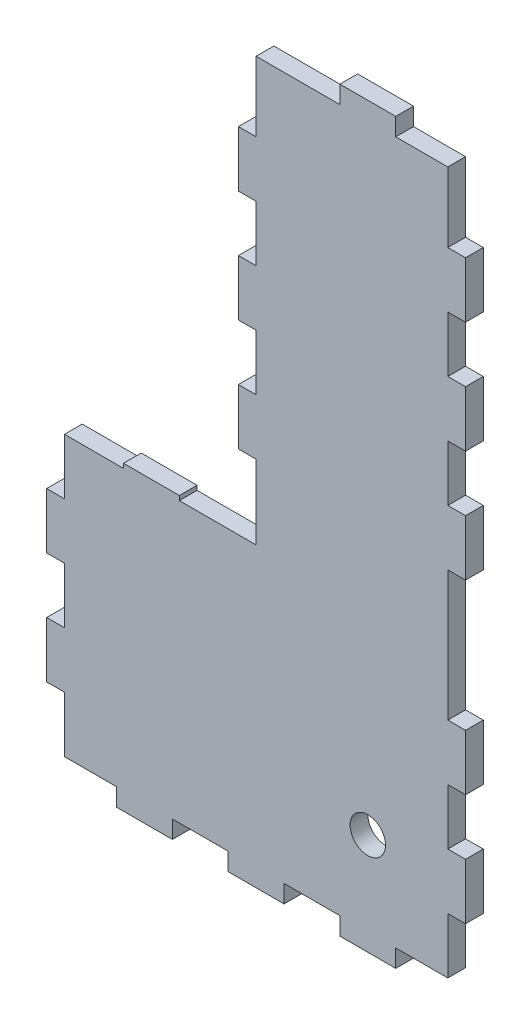
SolidWorks part; units mm, degrees
ref_plane "Front Plane" through (0, 0, 0) normal (0, 0, 1) x (1, 0, 0)
ref_plane "Top Plane" through (0, 0, 0) normal (0, 1, 0) x (1, 0, 0)
ref_plane "Right Plane" through (0, 0, 0) normal (1, 0, 0) x (0, 0, -1)
sketch "Sketch1" plane through (0, 0, 0) normal (0, 0, 1) x (1, 0, 0)
  line L0 (42.7349, 1.0135) -> (71.3849, 31.0135) construction
  line L1 (71.3849, 1.0135) -> (42.7349, 31.0135) construction
  line L2 (42.7349, 31.0135) -> (42.7349, 1.0135) construction
  line L3 (42.7349, 31.0135) -> (71.3849, 31.0135) construction
  line L144 (77.7349, 227.601) -> (77.7349, 252.601)
  line L145 (77.7349, 252.601) -> (71.3849, 252.601)
  line L146 (71.3849, 252.601) -> (71.3849, 227.601)
  line L147 (71.3849, 227.601) -> (77.7349, 227.601)
  line L148 (77.7349, 207.601) -> (77.7349, 227.601)
  line L149 (77.7349, 227.601) -> (71.3849, 227.601)
  line L150 (71.3849, 227.601) -> (71.3849, 207.601)
  line L151 (71.3849, 207.601) -> (77.7349, 207.601)
  line L152 (77.7349, 187.601) -> (77.7349, 207.601)
  line L153 (77.7349, 207.601) -> (71.3849, 207.601)
  line L154 (71.3849, 207.601) -> (71.3849, 187.601)
  line L155 (71.3849, 187.601) -> (77.7349, 187.601)
  line L156 (77.7349, 167.601) -> (77.7349, 187.601)
  line L157 (77.7349, 187.601) -> (71.3849, 187.601)
  line L158 (71.3849, 187.601) -> (71.3849, 167.601)
  line L159 (71.3849, 167.601) -> (77.7349, 167.601)
  line L160 (77.7349, 147.601) -> (77.7349, 167.601)
  line L161 (77.7349, 167.601) -> (71.3849, 167.601)
  line L162 (71.3849, 167.601) -> (71.3849, 147.601)
  line L163 (71.3849, 147.601) -> (77.7349, 147.601)
  line L164 (77.7349, 127.601) -> (77.7349, 147.601)
  line L165 (77.7349, 147.601) -> (71.3849, 147.601)
  line L166 (71.3849, 147.601) -> (71.3849, 127.601)
  line L167 (71.3849, 127.601) -> (77.7349, 127.601)
  line L168 (77.7349, 81.0135) -> (77.7349, 127.601)
  line L169 (77.7349, 127.601) -> (71.3849, 127.601)
  line L170 (71.3849, 127.601) -> (71.3849, 81.0135)
  line L171 (71.3849, 81.0135) -> (77.7349, 81.0135)
  line L172 (77.7349, 61.0135) -> (77.7349, 81.0135)
  line L173 (77.7349, 81.0135) -> (71.3849, 81.0135)
  line L174 (71.3849, 81.0135) -> (71.3849, 61.0135)
  line L175 (71.3849, 61.0135) -> (77.7349, 61.0135)
  line L176 (77.7349, 41.0135) -> (77.7349, 61.0135)
  line L177 (77.7349, 61.0135) -> (71.3849, 61.0135)
  line L178 (71.3849, 61.0135) -> (71.3849, 41.0135)
  line L179 (71.3849, 41.0135) -> (77.7349, 41.0135)
  line L180 (77.7349, 21.0135) -> (77.7349, 41.0135)
  line L181 (77.7349, 41.0135) -> (71.3849, 41.0135)
  line L182 (71.3849, 41.0135) -> (71.3849, 21.0135)
  line L183 (71.3849, 21.0135) -> (77.7349, 21.0135)
  line L184 (77.7349, 1.0135) -> (77.7349, 21.0135)
  line L185 (77.7349, 21.0135) -> (71.3849, 21.0135)
  line L186 (71.3849, 21.0135) -> (71.3849, 1.0135)
  line L187 (71.3849, 1.0135) -> (77.7349, 1.0135)
  line L188 (52.7349, -5.3365) -> (77.7349, -5.3365)
  line L189 (77.7349, -5.3365) -> (77.7349, 1.0135)
  line L190 (77.7349, 1.0135) -> (52.7349, 1.0135)
  line L191 (52.7349, 1.0135) -> (52.7349, -5.3365)
  line L192 (32.7349, -5.3365) -> (52.7349, -5.3365)
  line L193 (52.7349, -5.3365) -> (52.7349, 1.0135)
  line L194 (52.7349, 1.0135) -> (32.7349, 1.0135)
  line L195 (32.7349, 1.0135) -> (32.7349, -5.3365)
  line L196 (12.7349, -5.3365) -> (32.7349, -5.3365)
  line L197 (32.7349, -5.3365) -> (32.7349, 1.0135)
  line L198 (32.7349, 1.0135) -> (12.7349, 1.0135)
  line L199 (12.7349, 1.0135) -> (12.7349, -5.3365)
  line L200 (-7.2651, -5.3365) -> (12.7349, -5.3365)
  line L201 (12.7349, -5.3365) -> (12.7349, 1.0135)
  line L202 (12.7349, 1.0135) -> (-7.2651, 1.0135)
  line L203 (-7.2651, 1.0135) -> (-7.2651, -5.3365)
  line L204 (-27.2651, -5.3365) -> (-7.2651, -5.3365)
  line L205 (-7.2651, -5.3365) -> (-7.2651, 1.0135)
  line L206 (-7.2651, 1.0135) -> (-27.2651, 1.0135)
  line L207 (-27.2651, 1.0135) -> (-27.2651, -5.3365)
  line L208 (-47.2651, -5.3365) -> (-27.2651, -5.3365)
  line L209 (-27.2651, -5.3365) -> (-27.2651, 1.0135)
  line L210 (-27.2651, 1.0135) -> (-47.2651, 1.0135)
  line L211 (-47.2651, 1.0135) -> (-47.2651, -5.3365)
  line L212 (-72.2651, -5.3365) -> (-47.2651, -5.3365)
  line L213 (-47.2651, -5.3365) -> (-47.2651, 1.0135)
  line L214 (-47.2651, 1.0135) -> (-72.2651, 1.0135)
  line L215 (-72.2651, 1.0135) -> (-72.2651, -5.3365)
  line L216 (-65.9151, 1.0135) -> (-65.9151, 21.0135)
  line L217 (-65.9151, 21.0135) -> (-72.2651, 21.0135)
  line L218 (-72.2651, 21.0135) -> (-72.2651, 1.0135)
  line L219 (-72.2651, 1.0135) -> (-65.9151, 1.0135)
  line L220 (-65.9151, 21.0135) -> (-65.9151, 41.0135)
  line L221 (-65.9151, 41.0135) -> (-72.2651, 41.0135)
  line L222 (-72.2651, 41.0135) -> (-72.2651, 21.0135)
  line L223 (-72.2651, 21.0135) -> (-65.9151, 21.0135)
  line L224 (-65.9151, 41.0135) -> (-65.9151, 61.0135)
  line L225 (-65.9151, 61.0135) -> (-72.2651, 61.0135)
  line L226 (-72.2651, 61.0135) -> (-72.2651, 41.0135)
  line L227 (-72.2651, 41.0135) -> (-65.9151, 41.0135)
  line L228 (-65.9151, 61.0135) -> (-65.9151, 81.0135)
  line L229 (-65.9151, 81.0135) -> (-72.2651, 81.0135)
  line L230 (-72.2651, 81.0135) -> (-72.2651, 61.0135)
  line L231 (-72.2651, 61.0135) -> (-65.9151, 61.0135)
  line L232 (-65.9151, 81.0135) -> (-65.9151, 101.0135)
  line L233 (-65.9151, 101.0135) -> (-72.2651, 101.0135)
  line L234 (-72.2651, 101.0135) -> (-72.2651, 81.0135)
  line L235 (-72.2651, 81.0135) -> (-65.9151, 81.0135)
  line L236 (-72.2651, 101.0135) -> (-44.7651, 101.0135)
  line L237 (-44.7651, 101.0135) -> (-44.7651, 102.601)
  line L238 (-44.7651, 102.601) -> (-72.2651, 102.601)
  line L239 (-72.2651, 102.601) -> (-72.2651, 101.0135)
  line L240 (-44.7651, 101.0135) -> (-24.7651, 101.0135)
  line L241 (-24.7651, 101.0135) -> (-24.7651, 102.601)
  line L242 (-24.7651, 102.601) -> (-44.7651, 102.601)
  line L243 (-44.7651, 102.601) -> (-44.7651, 101.0135)
  line L244 (-24.7651, 101.0135) -> (2.7349, 101.0135)
  line L245 (2.7349, 101.0135) -> (2.7349, 102.601)
  line L246 (2.7349, 102.601) -> (-24.7651, 102.601)
  line L247 (-24.7651, 102.601) -> (-24.7651, 101.0135)
  line L248 (2.7349, 102.601) -> (2.7349, 127.601)
  line L249 (2.7349, 127.601) -> (-3.6151, 127.601)
  line L250 (-3.6151, 127.601) -> (-3.6151, 102.601)
  line L251 (-3.6151, 102.601) -> (2.7349, 102.601)
  line L252 (2.7349, 127.601) -> (2.7349, 147.601)
  line L253 (2.7349, 147.601) -> (-3.6151, 147.601)
  line L254 (-3.6151, 147.601) -> (-3.6151, 127.601)
  line L255 (-3.6151, 127.601) -> (2.7349, 127.601)
  line L256 (2.7349, 147.601) -> (2.7349, 167.601)
  line L257 (2.7349, 167.601) -> (-3.6151, 167.601)
  line L258 (-3.6151, 167.601) -> (-3.6151, 147.601)
  line L259 (-3.6151, 147.601) -> (2.7349, 147.601)
  line L260 (2.7349, 167.601) -> (2.7349, 187.601)
  line L261 (2.7349, 187.601) -> (-3.6151, 187.601)
  line L262 (-3.6151, 187.601) -> (-3.6151, 167.601)
  line L263 (-3.6151, 167.601) -> (2.7349, 167.601)
  line L264 (2.7349, 187.601) -> (2.7349, 207.601)
  line L265 (2.7349, 207.601) -> (-3.6151, 207.601)
  line L266 (-3.6151, 207.601) -> (-3.6151, 187.601)
  line L267 (-3.6151, 187.601) -> (2.7349, 187.601)
  line L268 (2.7349, 207.601) -> (2.7349, 227.601)
  line L269 (2.7349, 227.601) -> (-3.6151, 227.601)
  line L270 (-3.6151, 227.601) -> (-3.6151, 207.601)
  line L271 (-3.6151, 207.601) -> (2.7349, 207.601)
  line L272 (2.7349, 227.601) -> (2.7349, 252.601)
  line L273 (2.7349, 252.601) -> (-3.6151, 252.601)
  line L274 (-3.6151, 252.601) -> (-3.6151, 227.601)
  line L275 (-3.6151, 227.601) -> (2.7349, 227.601)
  line L276 (-3.6151, 252.601) -> (32.7349, 252.601)
  line L277 (32.7349, 252.601) -> (32.7349, 258.951)
  line L278 (32.7349, 258.951) -> (-3.6151, 258.951)
  line L279 (-3.6151, 258.951) -> (-3.6151, 252.601)
  line L280 (32.7349, 252.601) -> (52.7349, 252.601)
  line L281 (52.7349, 252.601) -> (52.7349, 258.951)
  line L282 (52.7349, 258.951) -> (32.7349, 258.951)
  line L283 (32.7349, 258.951) -> (32.7349, 252.601)
  line L284 (52.7349, 252.601) -> (77.7349, 252.601)
  line L285 (77.7349, 252.601) -> (77.7349, 258.951)
  line L286 (77.7349, 258.951) -> (52.7349, 258.951)
  line L287 (52.7349, 258.951) -> (52.7349, 252.601)
  circle A0 centre (42.7349, 31.0135) radius 19.1255
  circle A1 centre (42.7349, 31.0135) radius 6.35
  dimension "D1" = 38.2509
  dimension "D2" = 12.7
extrude "Boss-Extrude1" add sketch "Sketch1" against normal blind 6.35 contours L284 L280 L276 L272 L268 L264 L260 L256 L252 L248 L245 L244 L240 L236 L232 L228 L224 L220 L216 L214 L210 L206 L202 L198 L194 L190 L186 L182 L178 L174 L170 L166 L162 L158 L154 L150 L146 A0 | L241 L242 L237 L240 | L229 L230 L225 L228 | L221 L222 L217 L220 | L210 L211 L208 L207 | L202 L203 L200 L199 | L194 L195 L192 L191 | L182 L183 L180 L179 | L174 L175 L172 L171 | L166 L167 L164 L163 | L158 L159 L156 L155 | L150 L151 L148 L147 | L281 L282 L277 L280 | L269 L270 L265 L268 | L261 L262 L257 L260 | L253 L254 L249 L252 | A0 A1
